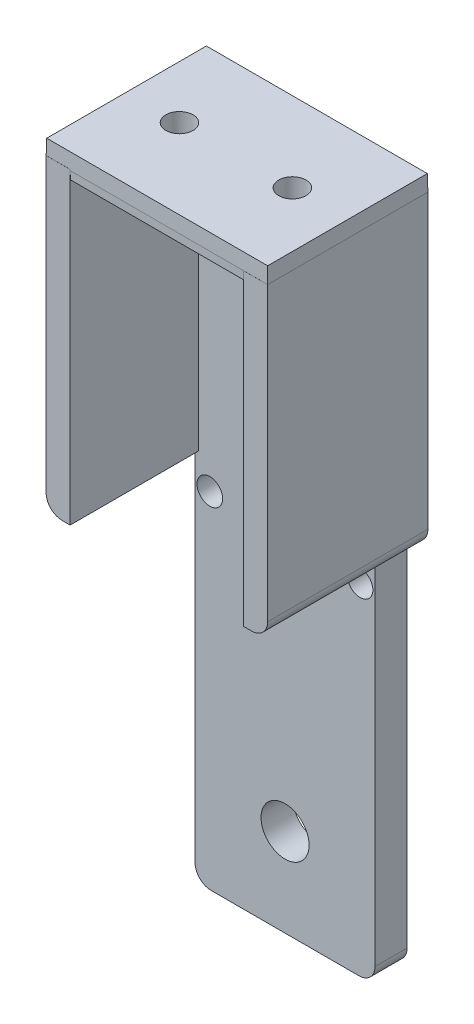
SolidWorks part; units mm, degrees
ref_plane "Plan de face" through (0, 0, 0) normal (0, 0, 1) x (1, 0, 0)
ref_plane "Plan de dessus" through (0, 0, 0) normal (0, 1, 0) x (1, 0, 0)
ref_plane "Plan de droite" through (0, 0, 0) normal (1, 0, 0) x (0, 0, -1)
sketch "Esquisse1" plane through (0, 0, 0) normal (0, 0, 1) x (1, 0, 0)
  line L1 (-11.225, 42.5) -> (11.225, 42.5)
  line L2 (-11.225, 42.5) -> (-11.225, -42.5)
  line L3 (-11.225, -42.5) -> (11.225, -42.5)
  line L4 (11.225, 42.5) -> (11.225, -42.5)
  line L5 (-11.225, 42.5) -> (11.225, -42.5) construction
  line L6 (-11.225, -42.5) -> (11.225, 42.5) construction
  point P0 (0, 0)
extrude "Boss.-Extru.1" add sketch "Esquisse1" along normal blind 4 contours L2 L1 L4 L3
sketch "Esquisse2" plane through (0, 0, 0) normal (0, 0, 1) x (1, 0, 0)
  line L0 (0, -42.5) -> (0, -31.5) construction
  line L2 (-11.225, -42.5) -> (11.225, -42.5) construction
  circle A0 centre (0, -31.5) radius 3
extrude "Enlèv. mat.-Extru.1" cut sketch "Esquisse2" along normal blind 4
sketch "Esquisse3" plane through (0, 0, 0) normal (0, 0, 1) x (1, 0, 0)
  circle A0 centre (-9.3915, 0.5498) radius 1.6
  circle A1 centre (9.3594, 0.0497) radius 1.6
extrude "Enlèv. mat.-Extru.2" cut sketch "Esquisse3" along normal blind 4
sketch "Esquisse4" plane through (0, 0, 0) normal (0, 0, 1) x (1, 0, 0)
  line L0 (0, -31.5) -> (0, 4.3) construction
  line L1 (-11.225, 42.5) -> (11.225, 42.5) construction
  line L2 (10.8256, 42.5) -> (13.8256, 42.5)
  line L3 (10.8256, 42.5) -> (10.8256, 4.0625)
  line L4 (10.8256, 4.0625) -> (13.8256, 4.0625)
  line L5 (13.8256, 42.5) -> (13.8256, 4.0625)
  line L10 (0, 4.3) -> (-11.225, 4.3) construction
  line L11 (-11.225, 42.5) -> (-11.225, -42.5) construction
  line L12 (-11.225, 4.3) -> (10.8256, 4.3) construction
  line L13 (-13.8173, 42.6266) -> (-10.8173, 42.6266)
  line L14 (-13.8173, 42.6266) -> (-13.8173, 4.1891)
  line L15 (-13.8173, 4.1891) -> (-10.8173, 4.1891)
  line L16 (-10.8173, 42.6266) -> (-10.8173, 4.1891)
extrude "Boss.-Extru.2" add sketch "Esquisse4" along normal blind 20
fillet "Congé1" radius 2 4 edges at (13.8256, 4.0625, 10) (-13.8173, 4.1891, 10) (11.225, -42.5, 2) (-11.225, -42.5, 2)
sketch "Esquisse7" plane through (0, 42.5, 0) normal (0, 1, 0) x (1, 0, 0)
  line L0 (-13.8173, -20) -> (-13.8173, 0) construction
  line L1 (13.8256, 0) -> (-13.8173, 0)
  line L2 (13.8256, 0) -> (13.8256, -19.9955)
  line L3 (13.8256, -19.9955) -> (-13.8173, -19.9955)
  line L4 (-13.8173, 0) -> (-13.8173, -19.9955)
extrude "Boss.-Extru.3" add sketch "Esquisse7" along normal blind 2 draft 1 and the other way blind 1 draft 1
sketch "Esquisse8" plane through (0, 0, 0) normal (0, 1, 0) x (1, 0, 0)
  line L0 (-13.7824, -9.9978) -> (13.7907, -9.9978) construction
  line L1 (-13.7824, -0.0349) -> (-13.7824, -19.9606) construction
  line L2 (13.7907, -19.9606) -> (13.7907, -0.0349) construction
  circle A0 centre (6.9136, -9.9978) radius 1.7
  circle A1 centre (-7.1784, -9.9978) radius 1.7
extrude "Enlèv. mat.-Extru.3" cut sketch "Esquisse8" along normal blind 58
